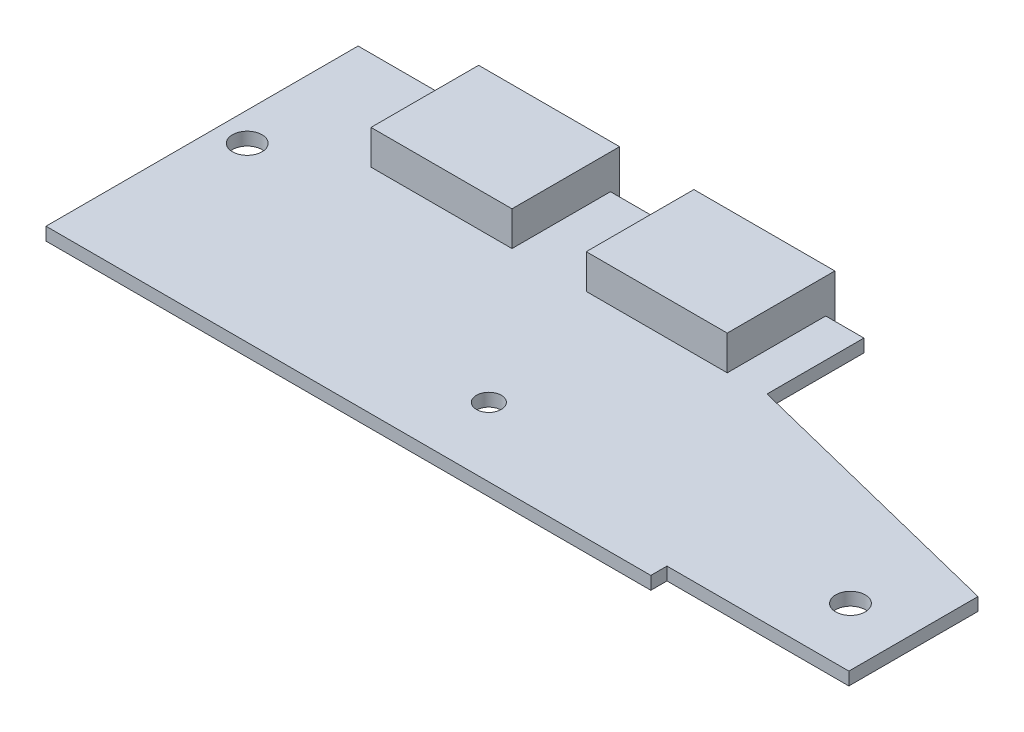
SolidWorks part; units mm, degrees
ref_plane "Спереди" through (0, 0, 0) normal (0, 0, 1) x (1, 0, 0)
ref_plane "Сверху" through (0, 0, 0) normal (0, 1, 0) x (1, 0, 0)
ref_plane "Справа" through (0, 0, 0) normal (1, 0, 0) x (0, 0, -1)
sketch "Эскиз1" plane through (0, 0, 0) normal (0, 1, 0) x (1, 0, 0)
  line L0 (0, 0) -> (-24540.967, 0) construction
  line L1 (0, 0) -> (0, 24540.967) construction
  line L2 (0, 0) -> (0, 29)
  line L3 (0, 29) -> (47, 29)
  line L4 (47, 29) -> (47, 20)
  line L5 (47, 20) -> (73.1, 13.5)
  line L6 (73.1, 13.5) -> (73.1, 1.5)
  line L7 (73.1, 1.5) -> (56.2, 1.5)
  line L8 (56.2, 1.5) -> (56.2, 0)
  line L9 (56.2, 0) -> (0, 0)
  point P7 (70.1456, 0)
  point P14 (83.4094, 3.367)
  dimension "D1" = 29
  dimension "D2" = 47
  dimension "D3" = 9
  dimension "D4" = 12
  dimension "D5" = 1.5
  dimension "D6" = 56.2
  dimension "D7" = 26.1
  dimension "D8" = 73.1
extrude "Бобышка-Вытянуть1" add sketch "Эскиз1" along normal blind 1.2
sketch "Эскиз2" plane through (0, 1.2, 0) normal (0, 1, 0) x (1, 0, 0)
  line L1 (0, 29) -> (0, 0) construction
  line L2 (0, 0) -> (56.2, 0) construction
  line L5 (73.1, 1.5) -> (73.1, 13.5) construction
  line L7 (56.2, 1.5) -> (73.1, 1.5) construction
  circle A0 centre (2.675, 16.025) radius 1.375
  circle A1 centre (67.725, 7.025) radius 1.375
  circle A2 centre (34.75, 6.4) radius 1.15
  dimension "D1" = 2.75
  dimension "D2" = 1.3
  dimension "D4" = 4
  dimension "D5" = 4.15
  dimension "D6" = 5.25
  dimension "D7" = 33.6
  dimension "D8" = 2.3
  dimension "D3" = 14.65
extrude "Вырез-Вытянуть1" cut sketch "Эскиз2" against normal through all
sketch "Эскиз3" plane through (0, 1.2, 0) normal (0, 1, 0) x (1, 0, 0)
  line L0 (47, 29) -> (0, 29) construction
  line L1 (10.35, 29.85) -> (23.45, 29.85)
  line L2 (10.35, 29.85) -> (10.35, 19.85)
  line L3 (10.35, 19.85) -> (23.45, 19.85)
  line L4 (23.45, 29.85) -> (23.45, 19.85)
  line L5 (30.35, 29.85) -> (43.45, 29.85)
  line L6 (30.35, 29.85) -> (30.35, 19.85)
  line L7 (30.35, 19.85) -> (43.45, 19.85)
  line L8 (43.45, 29.85) -> (43.45, 19.85)
  line L9 (0, 29) -> (0, 0) construction
  line L10 (47, 20) -> (47, 29) construction
  dimension "D1" = 13.1
  dimension "D2" = 10
  dimension "D3" = 0.85
  dimension "D4" = 6.9
  dimension "D5" = 10.35
  dimension "D6" = 3.55
extrude "Бобышка-Вытянуть2" add sketch "Эскиз3" along normal blind 3.2 and the other way blind 2.5
sketch "Эскиз4" plane through (0, 0, 0) normal (0, -1, 0) x (1, 0, 0)
  line L0 (0, 0) -> (56.2, 0) construction
  line L1 (15.5, -5.5) -> (20.8, -5.5)
  line L2 (15.5, -5.5) -> (15.5, -10.8)
  line L3 (15.5, -10.8) -> (20.8, -10.8)
  line L4 (20.8, -5.5) -> (20.8, -10.8)
  line L5 (0, -29) -> (0, 0) construction
  dimension "D1" = 5.3
  dimension "D2" = 10.8
  dimension "D3" = 20.8
extrude "Бобышка-Вытянуть3" add sketch "Эскиз4" along normal blind 5.5
